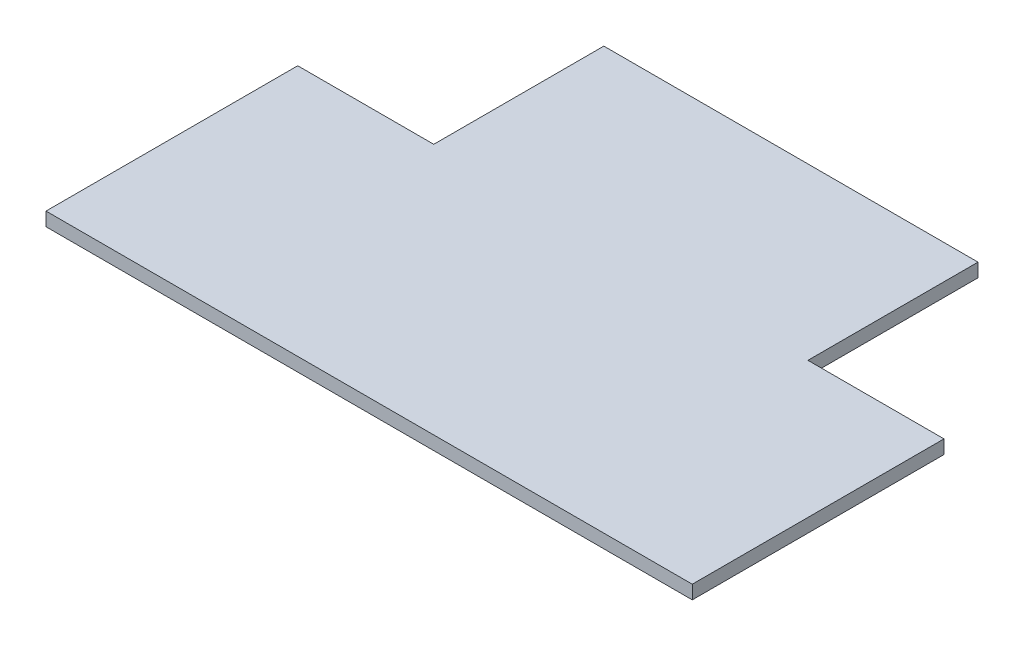
SolidWorks part; units mm, degrees
ref_plane "Alzado" through (0, 0, 0) normal (0, 0, 1) x (1, 0, 0)
ref_plane "Planta" through (0, 0, 0) normal (0, 1, 0) x (1, 0, 0)
ref_plane "Vista lateral" through (0, 0, 0) normal (1, 0, 0) x (0, 0, -1)
sketch "Croquis1" plane through (0, 0, 0) normal (0, 1, 0) x (1, 0, 0)
  line L0 (-75, -27.3994) -> (20, -27.3994)
  line L1 (-75, -27.3994) -> (-75, 9.6006)
  line L2 (-75, 9.6006) -> (-55, 9.6006)
  line L3 (-55, 9.6006) -> (-55, 34.6006)
  line L4 (-55, 34.6006) -> (0, 34.6006)
  line L5 (0, 34.6006) -> (0, 9.6006)
  line L6 (0, 9.6006) -> (20, 9.6006)
  line L7 (20, 9.6006) -> (20, -27.3994)
extrude "Saliente-Extruir1" add sketch "Croquis1" along normal blind 2
